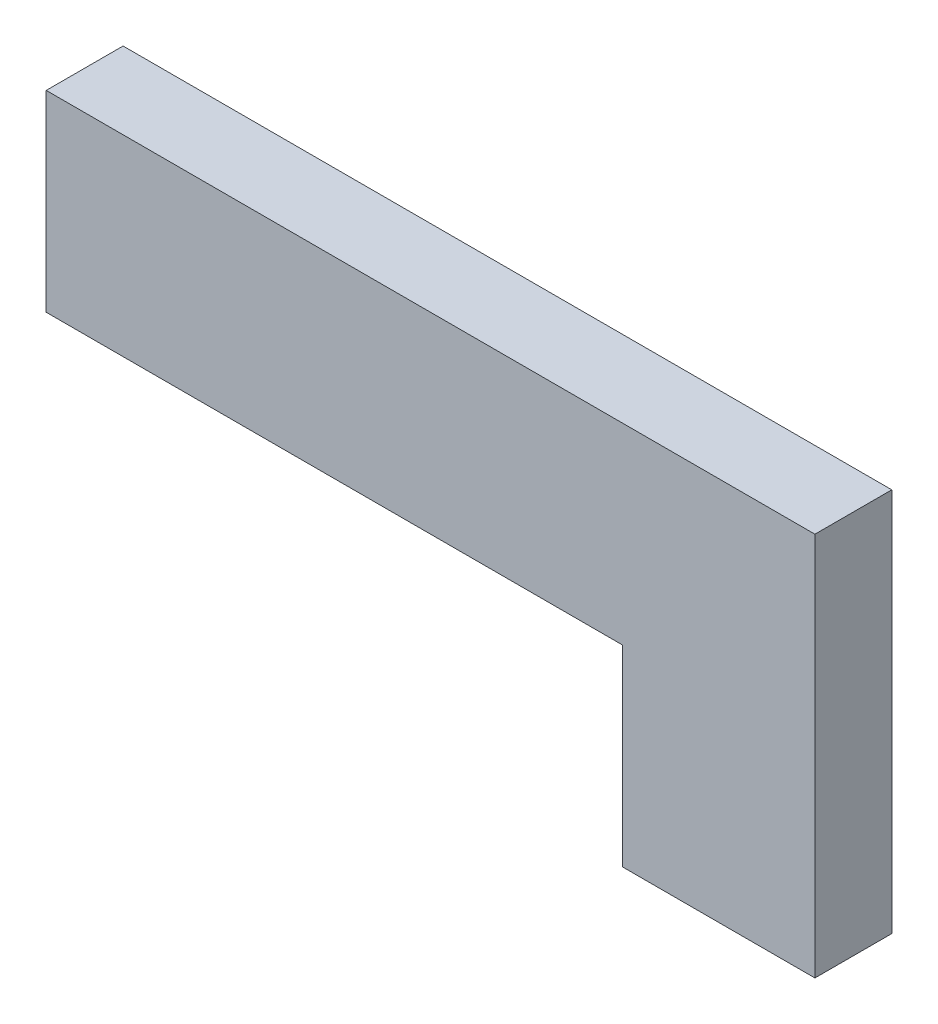
SolidWorks part; units mm, degrees
ref_plane "Front Plane" through (0, 0, 0) normal (0, 0, 1) x (1, 0, 0)
ref_plane "Top Plane" through (0, 0, 0) normal (0, 1, 0) x (1, 0, 0)
ref_plane "Right Plane" through (0, 0, 0) normal (1, 0, 0) x (0, 0, -1)
sketch "Sketch1" plane through (0, 0, 0) normal (0, 0, 1) x (1, 0, 0)
  line L0 (0, 0) -> (20, 0)
  line L1 (20, 0) -> (20, -10)
  line L2 (20, -10) -> (15, -10)
  line L3 (15, -10) -> (15, -5)
  line L4 (15, -5) -> (0, -5)
  line L5 (0, -5) -> (0, 0)
  dimension "D1" = 10
  dimension "D2" = 20
  dimension "D3" = 5
  dimension "D4" = 5
extrude "Boss-Extrude1" add sketch "Sketch1" along normal blind 2
